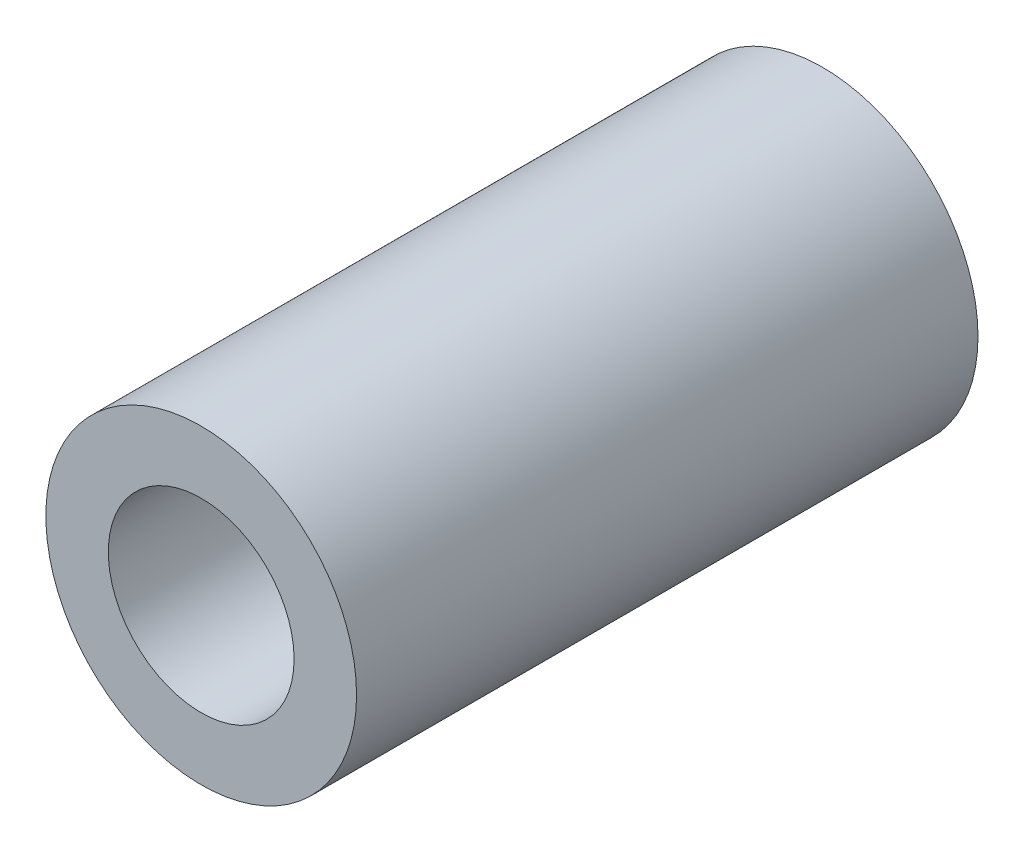
SolidWorks part; units mm, degrees
material "6061-T6 (SS)"
ref_plane "Front Plane" through (0, 0, 0) normal (0, 0, 1) x (1, 0, 0)
ref_plane "Top Plane" through (0, 0, 0) normal (0, 1, 0) x (1, 0, 0)
ref_plane "Right Plane" through (0, 0, 0) normal (1, 0, 0) x (0, 0, -1)
sketch "Sketch1" plane through (0, 0, 0) normal (0, 0, 1) x (1, 0, 0)
  circle A0 centre (0, 0) radius 3.175
  dimension "D1" = 6.35
extrude "Boss-Extrude1" add sketch "Sketch1" along normal blind 12.7
hole_wizard "#6 Clearance Hole1" positions "Sketch2" profile "Sketch3" hole size "#6" standard "ANSI Inch" end condition through all
sketch "Sketch2" plane through (0, 0, 12.7) normal (0, 0, 1) x (1, 0, 0)
  point P0 (0, 0)
sketch "Sketch3" plane through (0, 0, 12.7) normal (1, 0, 0) x (0, -1, 0)
  line L0 (0, 0) -> (0, 12.7)
  line L1 (0, 12.7) -> (1.8986, 12.7)
  line L2 (1.8986, 12.7) -> (1.8986, 0)
  line L5 (1.8986, 0) -> (0, 0)
  line L11 (0, -6.35) -> (0, 107.95) construction
  dimension "Thru Hole Dia." = 3.7973
  dimension "Thru Hole Depth" = 12.7
